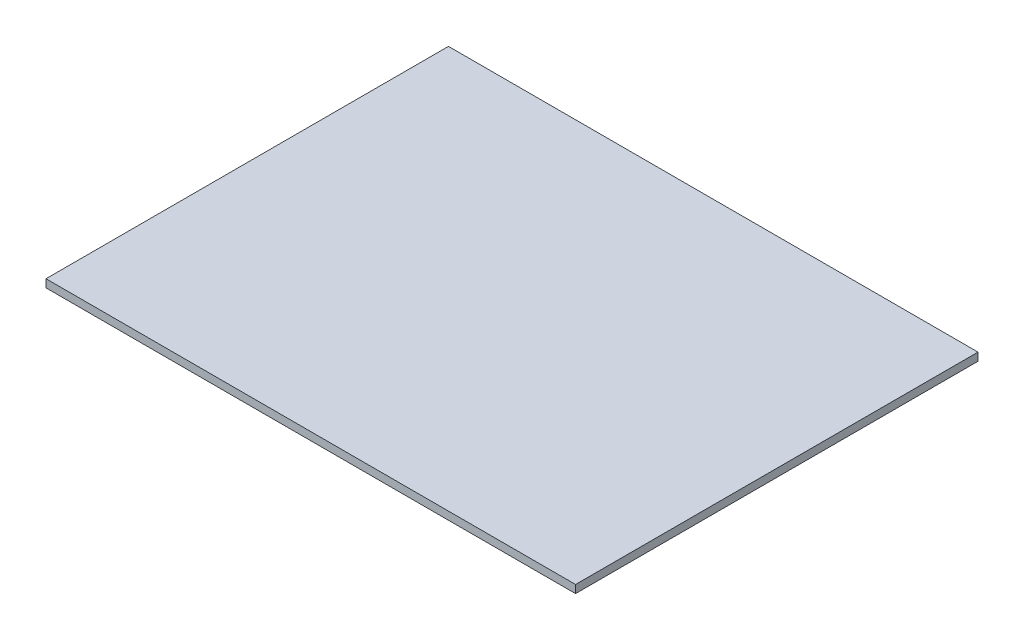
SolidWorks part; units mm, degrees
ref_plane "Front Plane" through (0, 0, 0) normal (0, 0, 1) x (1, 0, 0)
ref_plane "Top Plane" through (0, 0, 0) normal (0, 1, 0) x (1, 0, 0)
ref_plane "Right Plane" through (0, 0, 0) normal (1, 0, 0) x (0, 0, -1)
sketch "Sketch1" plane through (0, 0, 0) normal (0, 1, 0) x (1, 0, 0)
  line L0 (-100, 76) -> (-100, 0)
  line L1 (-100, 0) -> (0, 0)
  line L2 (0, 0) -> (0, 76)
  line L3 (0, 76) -> (-100, 76)
  dimension "D1" = 76
  dimension "D2" = 100
extrude "Boss-Extrude1" add sketch "Sketch1" along normal blind 1.5
